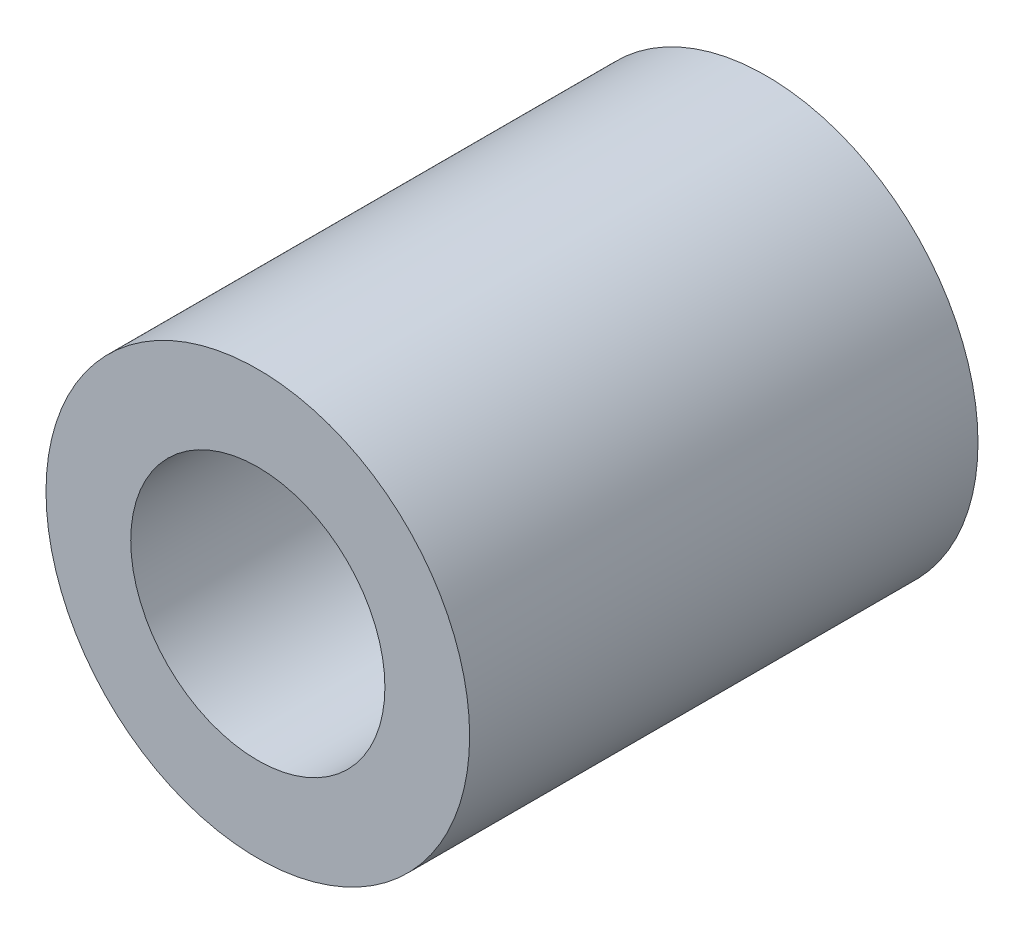
SolidWorks part; units mm, degrees
ref_plane "Front Plane" through (0, 0, 0) normal (0, 0, 1) x (1, 0, 0)
ref_plane "Top Plane" through (0, 0, 0) normal (0, 1, 0) x (1, 0, 0)
ref_plane "Right Plane" through (0, 0, 0) normal (1, 0, 0) x (0, 0, -1)
sketch "Sketch1" plane through (0, 0, 0) normal (0, 0, 1) x (1, 0, 0)
  circle A0 centre (0, 0) radius 2.5
  circle A1 centre (0, 0) radius 1.5
  dimension "D1" = 5
  dimension "D2" = 3
extrude "Boss-Extrude1" add sketch "Sketch1" along normal blind 6
